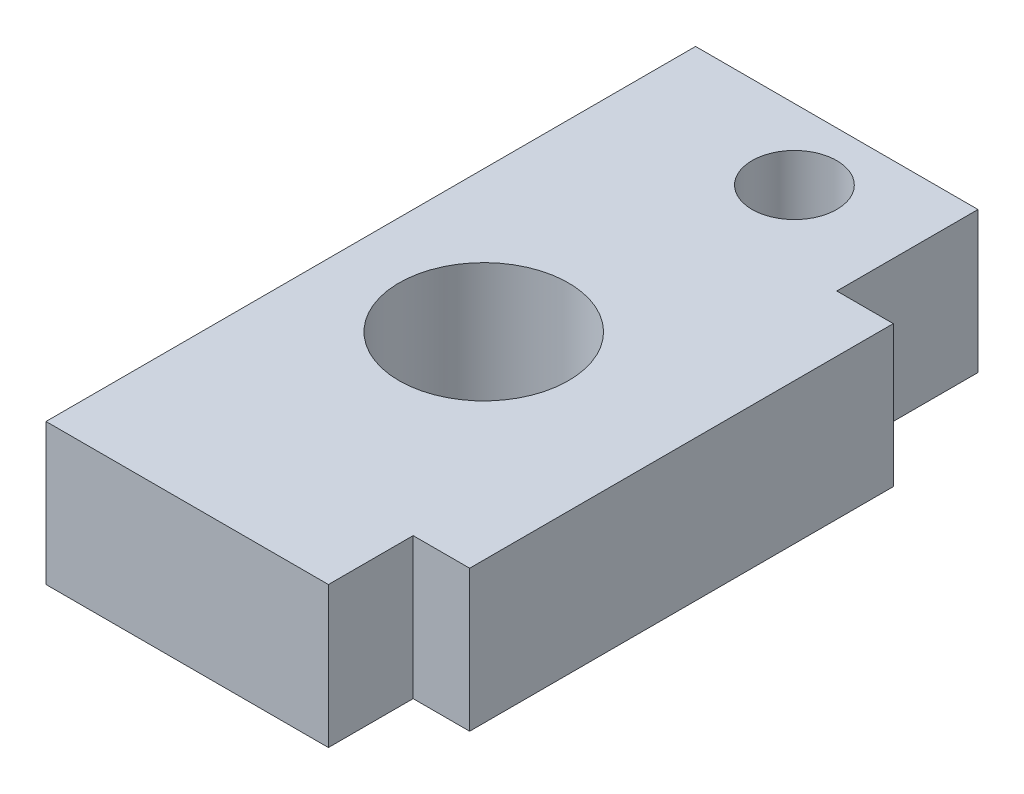
SolidWorks part; units mm, degrees
material "Balsa"
ref_plane "Plan de face" through (0, 0, 0) normal (0, 0, 1) x (1, 0, 0)
ref_plane "Plan de dessus" through (0, 0, 0) normal (0, 1, 0) x (1, 0, 0)
ref_plane "Plan de droite" through (0, 0, 0) normal (1, 0, 0) x (0, 0, -1)
sketch "Esquisse1" plane through (0, 0, 0) normal (0, 1, 0) x (1, 0, 0)
  line L1 (-5, 7.5) -> (7, 7.5)
  line L2 (-5, 7.5) -> (-5, -7.5)
  line L3 (-5, -7.5) -> (7, -7.5)
  line L4 (7, 7.5) -> (7, -7.5)
  dimension "D1" = 5
  dimension "D2" = 12
  dimension "D3" = 15
  dimension "D4" = 7.5
extrude "Boss.-Extru.1" add sketch "Esquisse1" along normal blind 5
sketch "Esquisse2" plane through (0, 5, 0) normal (0, 1, 0) x (1, 0, 0)
  line L0 (7, 7.5) -> (-5, 7.5) construction
  line L1 (5, 7.5) -> (-5, 7.5)
  line L2 (5, 7.5) -> (5, 12.5)
  line L3 (5, 12.5) -> (-5, 12.5)
  line L4 (-5, 7.5) -> (-5, 12.5)
  line L5 (-5, -7.5) -> (7, -7.5) construction
  line L6 (5, -7.5) -> (-5, -7.5)
  line L7 (5, -7.5) -> (5, -10.5)
  line L8 (5, -10.5) -> (-5, -10.5)
  line L9 (-5, -7.5) -> (-5, -10.5)
  dimension "D1" = 5
  dimension "D2" = 10
  dimension "D3" = 5
  dimension "D4" = 10
  dimension "D5" = 3
  dimension "D6" = 5
extrude "Boss.-Extru.2" add sketch "Esquisse2" against normal blind 5 contours L2 L3 L4 L1 | L8 L9 L6 L7
sketch "Esquisse3" plane through (0, 5, 0) normal (0, 1, 0) x (1, 0, 0)
  line L0 (7, 7.5) -> (5, 7.5) construction
  line L2 (-5, -10.5) -> (-5, 12.5) construction
  circle A0 centre (1, 10) radius 1.5
  dimension "D1" = 3
  dimension "D2" = 2.5
  dimension "D3" = 6
extrude "Enlèv. mat.-Extru.1" cut sketch "Esquisse3" against normal blind 5
sketch "Esquisse4" plane through (0, 5, 0) normal (0, 1, 0) x (1, 0, 0)
  line L0 (5, -10.5) -> (-5, -10.5) construction
  circle A0 centre (0, 0) radius 3
  dimension "D1" = 6
  dimension "droite/gauche" = 0
  dimension "D2" = 10.5
extrude "Enlèv. mat.-Extru.2" cut sketch "Esquisse4" against normal blind 10
